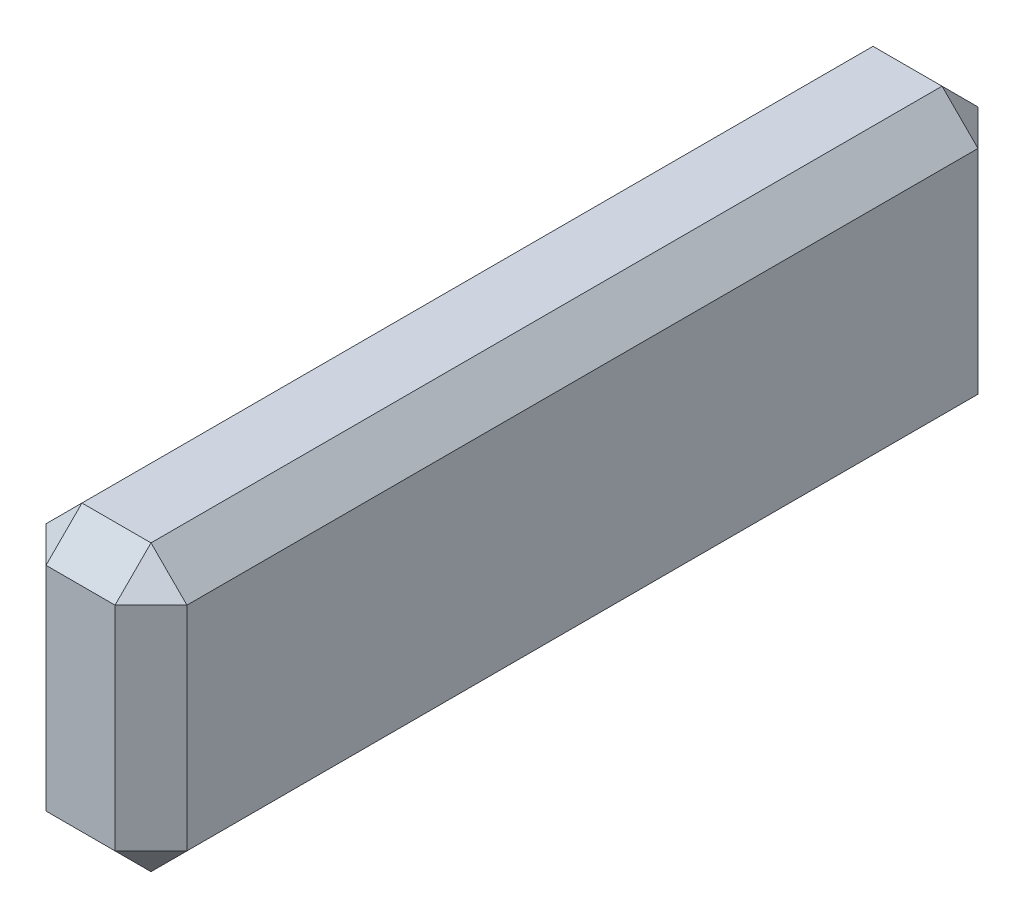
SolidWorks part; units mm, degrees
material "6061-T6 (SS)"
ref_plane "Front Plane" through (0, 0, 0) normal (0, 0, 1) x (1, 0, 0)
ref_plane "Top Plane" through (0, 0, 0) normal (0, 1, 0) x (1, 0, 0)
ref_plane "Right Plane" through (0, 0, 0) normal (1, 0, 0) x (0, 0, -1)
sketch "Sketch5" plane through (0, 0, 0) normal (0, 0, 1) x (1, 0, 0)
  line L1 (-3.1115, -6.2865) -> (3.1115, -6.2865)
  line L2 (-3.1115, -6.2865) -> (-3.1115, 6.2865)
  line L3 (-3.1115, 6.2865) -> (3.1115, 6.2865)
  line L4 (3.1115, -6.2865) -> (3.1115, 6.2865)
  line L5 (-3.1115, -6.2865) -> (3.1115, 6.2865) construction
  line L6 (-3.1115, 6.2865) -> (3.1115, -6.2865) construction
  point P0 (0, 0)
  dimension "D1" = 6.223
  dimension "D2" = 12.573
extrude "Boss-Extrude3" add sketch "Sketch5" along normal blind 38.1
chamfer "Chamfer1" distance 1.5875 angle 45 12 edges at (0, -6.2865, 0) (-3.1115, -6.2865, 19.05) (-3.1115, 0, 0) (-3.1115, 6.2865, 19.05) (0, 6.2865, 0) (3.1115, -6.2865, 19.05) (3.1115, 0, 0) (3.1115, 6.2865, 19.05) (0, -6.2865, 38.1) (-3.1115, 0, 38.1) (0, 6.2865, 38.1) (3.1115, 0, 38.1)
